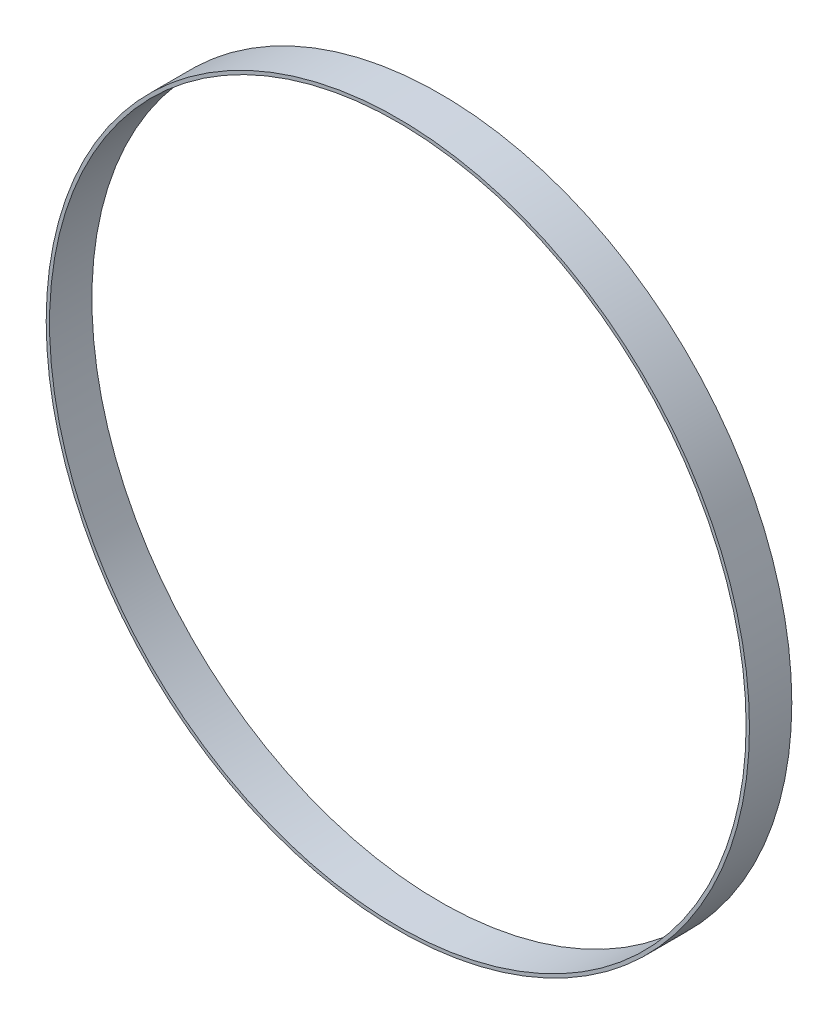
SolidWorks part; units mm, degrees
material "EPDM 60 Durometer"
ref_plane "Front" through (0, 0, 0) normal (0, 0, 1) x (1, 0, 0)
ref_plane "Top" through (0, 0, 0) normal (0, 1, 0) x (1, 0, 0)
ref_plane "Right" through (0, 0, 0) normal (1, 0, 0) x (0, 0, -1)
sketch "Sketch1" plane through (0, 0, 0) normal (0, 0, 1) x (1, 0, 0)
  circle A0 centre (0, 0) radius 83.05
  circle A2 centre (0, 0) radius 82.2563
  dimension "D1" = 166.1
  dimension "D2" = 0.7937
extrude "Boss-Extrude1" add sketch "Sketch1" along normal blind 10
